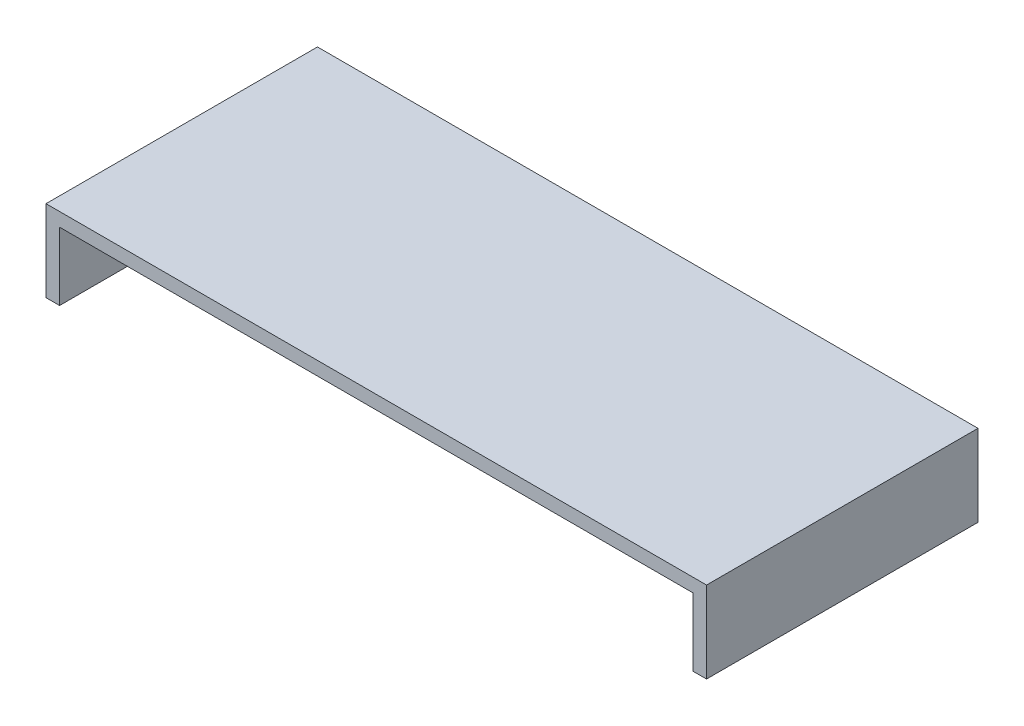
SolidWorks part; units mm, degrees
ref_plane "Front Plane" through (0, 0, 0) normal (0, 0, 1) x (1, 0, 0)
ref_plane "Top Plane" through (0, 0, 0) normal (0, 1, 0) x (1, 0, 0)
ref_plane "Right Plane" through (0, 0, 0) normal (1, 0, 0) x (0, 0, -1)
sketch "Sketch1" plane through (0, 0, 0) normal (0, 1, 0) x (1, 0, 0)
  line L1 (0, 0) -> (0.146, 0)
  line L2 (0, 0) -> (0, 0.06)
  line L3 (0, 0.06) -> (0.146, 0.06)
  line L4 (0.146, 0) -> (0.146, 0.06)
  dimension "D1" = 0.146
  dimension "D2" = 0.06
extrude "Boss-Extrude1" add sketch "Sketch1" along normal blind 0.018
sketch "Sketch4" plane through (0, 0, 0) normal (0, -1, 0) x (1, 0, 0)
  line L0 (0, 0) -> (0.146, 0) construction
  line L1 (0.003, 0) -> (0.143, 0)
  line L2 (0.003, 0) -> (0.003, -0.06)
  line L3 (0.003, -0.06) -> (0.143, -0.06)
  line L4 (0.143, 0) -> (0.143, -0.06)
  line L5 (0.146, -0.06) -> (0, -0.06) construction
  dimension "D1" = 0.003
  dimension "D2" = 0.003
extrude "Cut-Extrude1" cut sketch "Sketch4" against normal blind 0.015
